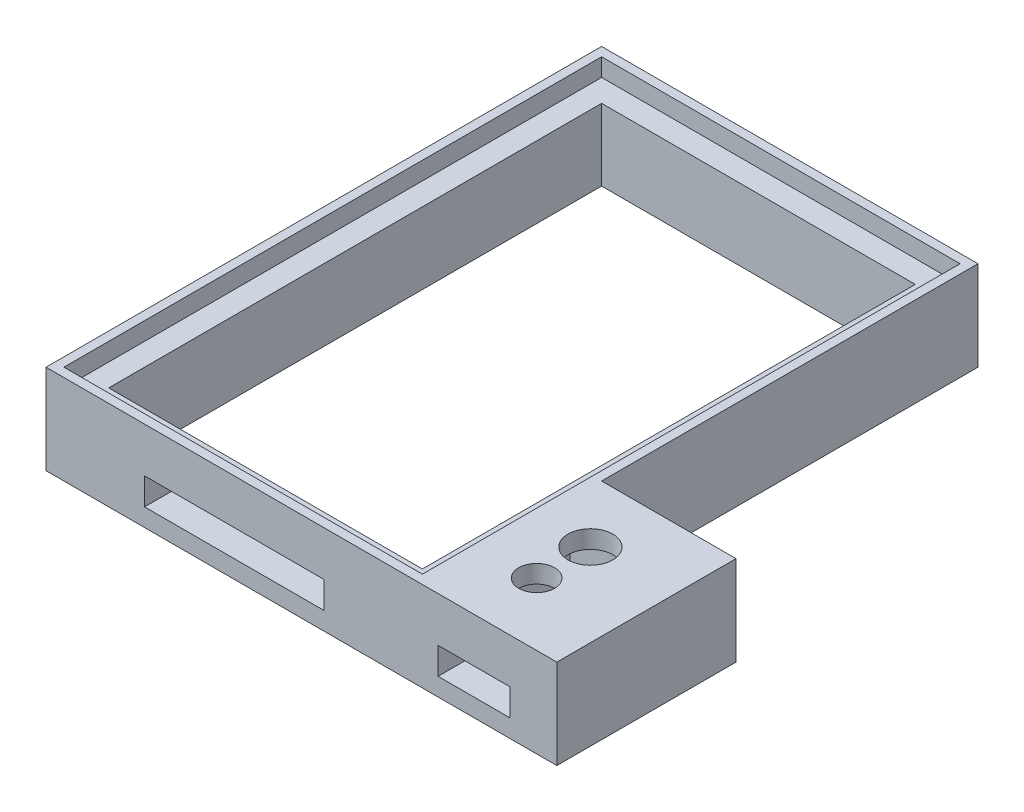
SolidWorks part; units mm, degrees
ref_plane "Alzado" through (0, 0, 0) normal (0, 0, 1) x (1, 0, 0)
ref_plane "Planta" through (0, 0, 0) normal (0, 1, 0) x (1, 0, 0)
ref_plane "Vista lateral" through (0, 0, 0) normal (1, 0, 0) x (0, 0, -1)
sketch "Croquis1" plane through (0, 0, 0) normal (0, 1, 0) x (1, 0, 0)
  line L1 (-21, -31) -> (21, -31)
  line L2 (-21, -31) -> (-21, 31)
  line L3 (-21, 31) -> (21, 31)
  line L4 (21, -31) -> (21, 31)
  line L5 (-21, -31) -> (21, 31) construction
  line L6 (-21, 31) -> (21, -31) construction
  point P0 (0, 0)
  dimension "D1" = 42
  dimension "D2" = 62
extrude "Saliente-Extruir1" add sketch "Croquis1" along normal blind 10
sketch "Croquis2" plane through (0, 10, 0) normal (0, 1, 0) x (1, 0, 0)
  line L1 (-20, -30) -> (20, -30)
  line L2 (-20, -30) -> (-20, 30)
  line L3 (-20, 30) -> (20, 30)
  line L4 (20, -30) -> (20, 30)
  line L5 (-20, -30) -> (20, 30) construction
  line L6 (-20, 30) -> (20, -30) construction
  point P0 (0, 0)
  dimension "D1" = 60
  dimension "D2" = 40
extrude "Cortar-Extruir1" cut sketch "Croquis2" against normal blind 2
sketch "Croquis3" plane through (0, 8, 0) normal (0, 1, 0) x (1, 0, 0)
  line L1 (17.5, -27.5) -> (-17.5, -27.5)
  line L2 (17.5, -27.5) -> (17.5, 27.5)
  line L3 (17.5, 27.5) -> (-17.5, 27.5)
  line L4 (-17.5, -27.5) -> (-17.5, 27.5)
  line L5 (17.5, -27.5) -> (-17.5, 27.5) construction
  line L6 (17.5, 27.5) -> (-17.5, -27.5) construction
  point P0 (0, 0)
  dimension "D1" = 35
  dimension "D2" = 55
extrude "Cortar-Extruir2" cut sketch "Croquis3" against normal blind 8
sketch "Croquis4" plane through (0, 0, 31) normal (0, 0, 1) x (1, 0, 0)
  line L0 (-21, 0) -> (21, 0) construction
  line L1 (-10, 2) -> (10, 2)
  line L2 (-10, 2) -> (-10, 5)
  line L3 (-10, 5) -> (10, 5)
  line L4 (10, 2) -> (10, 5)
  line L5 (-10, 2) -> (10, 5) construction
  line L6 (-10, 5) -> (10, 2) construction
  point P0 (0, 3.5)
  dimension "D1" = 20
  dimension "D2" = 0
  dimension "D3" = 3
  dimension "D4" = 2
extrude "Cortar-Extruir3" cut sketch "Croquis4" against normal blind 8
sketch "Croquis5" plane through (21, 0, 0) normal (1, 0, 0) x (0, 0, -1)
  line L0 (-31, 10) -> (31, 10) construction
  line L1 (-31, 0) -> (-11, 0)
  line L2 (-31, 0) -> (-31, 10)
  line L3 (-31, 10) -> (-11, 10)
  line L4 (-11, 0) -> (-11, 10)
  dimension "D1" = 20
extrude "Saliente-Extruir2" add sketch "Croquis5" along normal blind 15
sketch "Croquis6" plane through (0, 0, 0) normal (0, -1, 0) x (-1, 0, 0)
  line L0 (-36, -11) -> (-21, -11) construction
  line L1 (-21, -14.5) -> (-32.5, -14.5)
  line L2 (-21, -14.5) -> (-21, -27.5)
  line L3 (-21, -27.5) -> (-32.5, -27.5)
  line L4 (-32.5, -14.5) -> (-32.5, -27.5)
  line L6 (17.5, -27.5) -> (-17.5, -27.5) construction
  line L8 (-36, -31) -> (-36, -11) construction
  line L9 (-21, -11) -> (-21, 31) construction
  dimension "D1" = 3.5
  dimension "D2" = 0
  dimension "D3" = 3.5
  dimension "D4" = 0
extrude "Cortar-Extruir4" cut sketch "Croquis6" against normal blind 8
sketch "Croquis7" plane through (0, 10, 0) normal (0, 1, 0) x (1, 0, 0)
  line L0 (36, -11) -> (36, -31) construction
  line L1 (36, -11) -> (21, -11) construction
  line L2 (-21, -31) -> (36, -31) construction
  circle A0 centre (26.75, -18) radius 2.5
  circle A1 centre (26.75, -24) radius 2
  point P10 (0, 0)
  dimension "D1" = 9.25
  dimension "D3" = 7
  dimension "D2" = 7
  dimension "D4" = 9.25
extrude "Cortar-Extruir5" cut sketch "Croquis7" against normal blind 8
sketch "Croquis8" plane through (0, 0, 31) normal (0, 0, 1) x (1, 0, 0)
  line L0 (36, 10) -> (36, 0) construction
  line L1 (22.75, 2) -> (30.75, 2)
  line L2 (22.75, 2) -> (22.75, 5)
  line L3 (22.75, 5) -> (30.75, 5)
  line L4 (30.75, 2) -> (30.75, 5)
  line L5 (22.75, 2) -> (30.75, 5) construction
  line L6 (22.75, 5) -> (30.75, 2) construction
  line L7 (-10, 2) -> (10, 2) construction
  point P0 (26.75, 3.5)
  dimension "D1" = 9.25
  dimension "D2" = 8
  dimension "D3" = 3
  dimension "D4" = 0
extrude "Cortar-Extruir6" cut sketch "Croquis8" against normal blind 8
